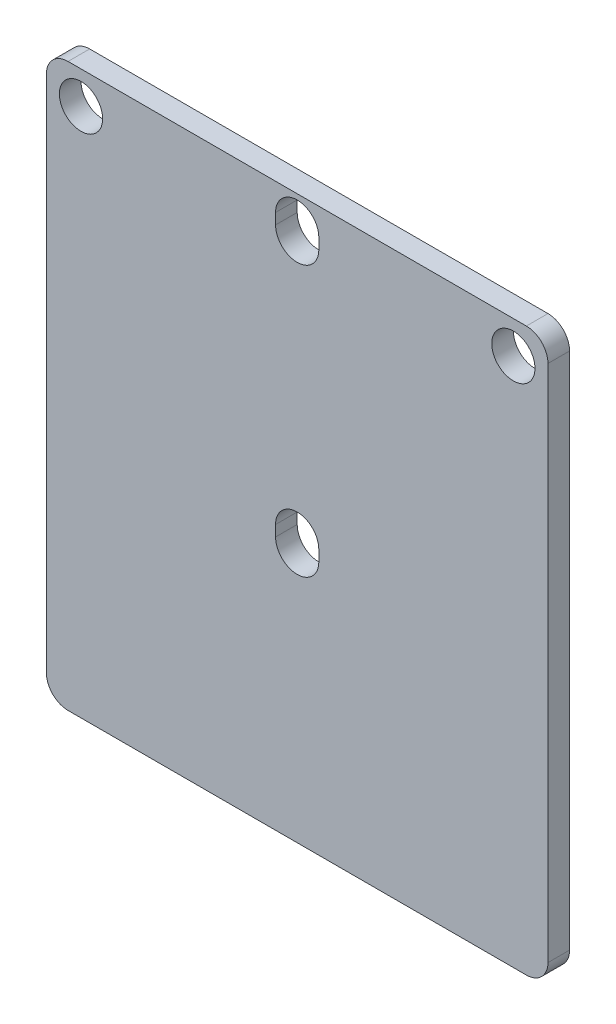
SolidWorks part; units mm, degrees
material "PVC 0.007 plastifié"
ref_plane "Face" through (0, 0, 0) normal (0, 0, 1) x (1, 0, 0)
ref_plane "Dessus" through (0, 0, 0) normal (0, 1, 0) x (1, 0, 0)
ref_plane "Droite" through (0, 0, 0) normal (1, 0, 0) x (0, 0, -1)
sketch "Esquisse1" plane through (0, 0, 0) normal (0, 0, 1) x (1, 0, 0)
  line L0 (0, 0) -> (33.0541, 0) construction
  line L1 (-23.2, 26) -> (23.2, 26)
  line L2 (-23.2, 26) -> (-23.2, -26)
  line L3 (-23.2, -26) -> (23.2, -26)
  line L4 (23.2, 26) -> (23.2, -26)
  line L5 (0, 0) -> (0, 31.1956) construction
  dimension "D1" = 46.4
  dimension "D2" = 52
extrude "Extrusion1" add sketch "Esquisse1" along normal blind 2
sketch "Esquisse2" plane through (0, 0, 2) normal (0, 0, 1) x (1, 0, 0)
  line L0 (0, 0) -> (0, 28.1312) construction
  line L1 (23.2, 26) -> (-23.2, 26) construction
  circle A0 centre (-20, 23) radius 2
  circle A1 centre (20, 23) radius 2
  dimension "D1" = 4
  dimension "D2" = 20
  dimension "D3" = 3
extrude "Enlèv. mat.-Extru.1" cut sketch "Esquisse2" against normal through all
sketch "Esquisse3" plane through (0, 0, 2) normal (0, 0, 1) x (1, 0, 0)
  line L0 (0, 0) -> (0, 30.0242) construction
  line L1 (2, 23.5) -> (2, 22.5)
  line L2 (-2, 23.5) -> (-2, 22.5)
  line L3 (23.2, 26) -> (-23.2, 26) construction
  line L4 (2, -1.5) -> (2, -2.5)
  line L5 (-2, -1.5) -> (-2, -2.5)
  line L6 (0, -25) -> (0, 5.0242) construction
  line L7 (23.2, -26) -> (23.2, 26) construction
  arc A0 (2, 23.5) -> (-2, 23.5) centre (0, 23.5) ccw
  arc A1 (-2, 22.5) -> (2, 22.5) centre (0, 22.5) ccw
  arc A2 (2, -1.5) -> (-2, -1.5) centre (0, -1.5) ccw
  arc A3 (-2, -2.5) -> (2, -2.5) centre (0, -2.5) ccw
  dimension "D1" = 4
  dimension "D2" = 4
  dimension "D3" = 1
  dimension "D4" = 22.5
  dimension "D5" = 24
extrude "Enlèv. mat.-Extru.2" cut sketch "Esquisse3" against normal through all
fillet "Congé1" radius 2 4 edges at (-23.2, -26, 1) (23.2, -26, 1) (23.2, 26, 1) (-23.2, 26, 1)
